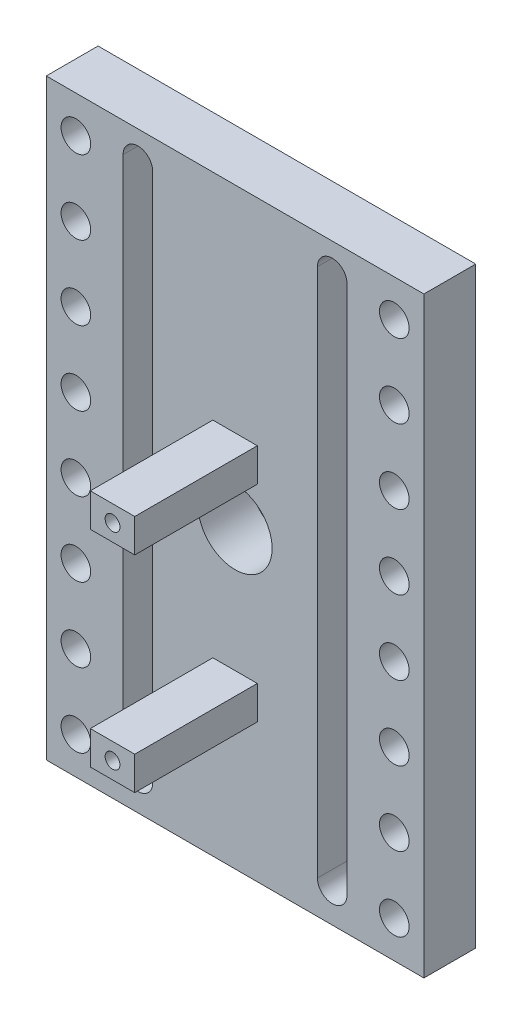
SolidWorks part; units mm, degrees
ref_plane "Front Plane" through (0, 0, 0) normal (0, 0, 1) x (1, 0, 0)
ref_plane "Top Plane" through (0, 0, 0) normal (0, 1, 0) x (1, 0, 0)
ref_plane "Right Plane" through (0, 0, 0) normal (1, 0, 0) x (0, 0, -1)
sketch "Sketch1" plane through (0, 0, 0) normal (0, 0, 1) x (1, 0, 0)
  line L1 (-17.5, 40) -> (17.5, 40)
  line L2 (-17.5, 40) -> (-17.5, -40)
  line L3 (-17.5, -40) -> (17.5, -40)
  line L4 (17.5, 40) -> (17.5, -40)
  line L5 (-17.5, 40) -> (17.5, -40) construction
  line L6 (-17.5, -40) -> (17.5, 40) construction
  point P0 (0, 0)
  dimension "D1" = 80
  dimension "D2" = 35
extrude "Boss-Extrude1" add sketch "Sketch1" along normal blind 7
sketch "Sketch2" plane through (0, 0, 7) normal (0, 0, 1) x (1, 0, 0)
  line L0 (-17.5, 0) -> (17.5, 0) construction
  line L1 (-17.5, 40) -> (-17.5, -40) construction
  line L2 (17.5, -40) -> (17.5, 40) construction
  line L4 (-7.5, 8.75) -> (7.5, 8.75) construction
  line L5 (-7.5, 8.75) -> (-7.5, -19.05) construction
  line L6 (-7.5, -19.05) -> (7.5, -19.05) construction
  line L7 (7.5, 8.75) -> (7.5, -19.05) construction
  line L8 (-3, 11) -> (3, 11)
  line L9 (-3, 11) -> (-3, 6.5)
  line L10 (-3, 6.5) -> (3, 6.5)
  line L11 (3, 11) -> (3, 6.5)
  line L12 (-3, 11) -> (3, 6.5) construction
  line L13 (-3, 6.5) -> (3, 11) construction
  line L14 (-3, -16.8) -> (3, -16.8)
  line L15 (-3, -16.8) -> (-3, -21.3)
  line L16 (-3, -21.3) -> (3, -21.3)
  line L17 (3, -16.8) -> (3, -21.3)
  line L18 (-3, -16.8) -> (3, -21.3) construction
  line L19 (-3, -21.3) -> (3, -16.8) construction
  circle A0 centre (0, 0) radius 2.45 construction
  circle A1 centre (0, 8.75) radius 1
  circle A2 centre (0, -19.05) radius 1
  point P13 (0, 8.75)
  point P20 (0, 0)
  dimension "D1" = 4.9
  dimension "D4" = 2
  dimension "D2" = 8.75
  dimension "D3" = 27.8
  dimension "D5" = 15
  dimension "D6" = 6
  dimension "D7" = 4.5
extrude "Boss-Extrude2" add sketch "Sketch2" along normal blind 16.55
sketch "Sketch3" plane through (0, 0, 7) normal (0, 0, 1) x (1, 0, 0)
  circle A0 centre (0, 0) radius 5
  dimension "D1" = 10
extrude "Cut-Extrude1" cut sketch "Sketch3" against normal blind 7
sketch "Sketch4" plane through (0, 0, 7) normal (0, 0, 1) x (1, 0, 0)
  line L0 (-13.12, 36) -> (-13.12, -35.5) construction
  line L1 (-11.12, 36) -> (-11.12, -35.5)
  line L2 (-15.12, 36) -> (-15.12, -35.5)
  line L3 (-17.5, 40) -> (-17.5, -40) construction
  line L4 (17.5, 40) -> (-17.5, 40) construction
  line L7 (0, 40) -> (0, -40) construction
  line L8 (-17.5, -40) -> (17.5, -40) construction
  line L9 (13.12, 36) -> (13.12, -35.5) construction
  line L10 (11.12, 36) -> (11.12, -35.5)
  line L11 (15.12, 36) -> (15.12, -35.5)
  arc A0 (-11.12, 36) -> (-15.12, 36) centre (-13.12, 36) ccw
  arc A1 (-15.12, -35.5) -> (-11.12, -35.5) centre (-13.12, -35.5) ccw
  arc A2 (11.12, 36) -> (15.12, 36) centre (13.12, 36) cw
  arc A3 (15.12, -35.5) -> (11.12, -35.5) centre (13.12, -35.5) cw
  point P2 (-13.12, 0.25)
  point P19 (13.12, 0.25)
  dimension "D4" = 2
  dimension "D1" = 4.38
  dimension "D2" = 4
  dimension "D3" = 71.5
extrude "Cut-Extrude2" cut sketch "Sketch4" against normal blind 15
sketch "Sketch5" plane through (0, 0, 7) normal (0, 0, 1) x (1, 0, 0)
  line L0 (17.5, 40) -> (-17.5, 40) construction
  line L1 (17.5, -40) -> (25.5, -40)
  line L2 (17.5, -40) -> (17.5, 40)
  line L3 (17.5, 40) -> (25.5, 40)
  line L4 (25.5, -40) -> (25.5, 40)
  line L5 (15.12, -35.5) -> (15.12, 36) construction
  line L6 (3, 11) -> (-3, 11) construction
  circle A0 centre (21.5, 35) radius 2
  circle A1 centre (21.5, 25) radius 2
  circle A2 centre (21.5, 15) radius 2
  circle A3 centre (21.5, 5) radius 2
  circle A4 centre (21.5, -5) radius 2
  circle A5 centre (21.5, -15) radius 2
  circle A6 centre (21.5, -25) radius 2
  circle A7 centre (21.5, -35) radius 2
  point P10 (21.5, 40)
  dimension "D1" = 4
  dimension "D2" = 5
  dimension "D3" = 8
  dimension "D5" = 12.12
  dimension "D6" = 4
  dimension "D8" = 25
  dimension "D4" = 8
extrude "Boss-Extrude3" add sketch "Sketch5" against normal blind 7
mirror "Mirror1" about plane through (0, 0, 0) normal (1, 0, 0) of "Boss-Extrude3"
